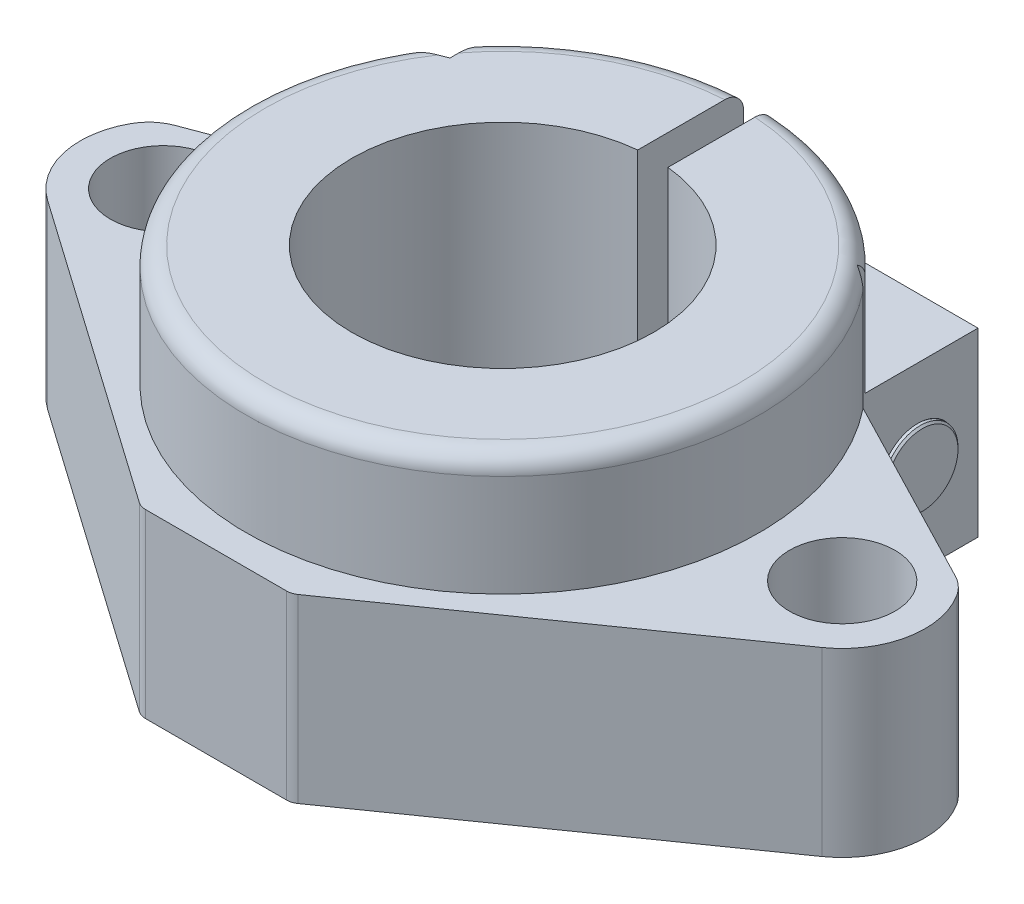
SolidWorks part; units mm, degrees
other "Markup1"
sketch "Sketch30" plane through (-28, 20, 19) normal (-0.8662, 0.4948, 0.0704) x (0.294, 0.3906, 0.8723)
ref_plane "Front Plane" through (0, 0, 0) normal (0, 0, 1) x (1, 0, 0)
ref_plane "Top Plane" through (0, 0, 0) normal (0, 1, 0) x (1, 0, 0)
ref_plane "Right Plane" through (0, 0, 0) normal (1, 0, 0) x (0, 0, -1)
sketch "Sketch1" plane through (0, 0, 0) normal (0, 1, 0) x (1, 0, 0)
  line L0 (0, 23.9567) -> (0, -22.6932) construction
  line L1 (-26.4411, 0) -> (25.427, 0) construction
  line L2 (5, -19) -> (-5, -19)
  line L3 (12.5, 19) -> (-12.5, 19)
  line L4 (-12.5, 19) -> (-26.5485, 3.7229)
  line L5 (-5, -19) -> (-25.6594, -4.502)
  line L6 (5, -19) -> (25.6594, -4.502)
  line L7 (12.5, 19) -> (26.5485, 3.7229)
  circle A1 centre (0, 0) radius 10 construction
  circle A2 centre (-22.5, 0) radius 3.5
  arc A3 (-26.5485, 3.7229) -> (-25.6594, -4.502) centre (-22.5, 0) ccw
  circle A4 centre (22.5, 0) radius 3.5
  arc A5 (26.5485, 3.7229) -> (25.6594, -4.502) centre (22.5, 0) cw
  point P20 (0, -19)
  point P21 (0, 19)
  dimension "D1" = 20
  dimension "D2" = 7
  dimension "D4" = 11
  dimension "D3" = 22.5
  dimension "D5" = 25
  dimension "D6" = 10
  dimension "D7" = 19
  dimension "D8" = 19
extrude "Boss-Extrude1" add sketch "Sketch1" along normal blind 12
sketch "Sketch3" plane through (0, 12, 0) normal (0, 1, 0) x (1, 0, 0)
  circle A0 centre (0, 0) radius 17
  dimension "D1" = 34
extrude "Boss-Extrude2" add sketch "Sketch3" along normal blind 8
fillet "Fillet1" radius 1.25 1 edges at (0, 20, 17)
sketch "Sketch2" plane through (0, 12, 0) normal (0, 1, 0) x (1, 0, 0)
  line L0 (12.5, 19) -> (12.5, 11)
  line L1 (12.5, 11) -> (26.5485, 3.7229)
  line L2 (26.5485, 3.7229) -> (12.5, 19)
  line L3 (-12.5, 19) -> (-12.5, 8.9996)
  line L4 (-12.5, 8.9996) -> (-26.5485, 3.7229)
  line L5 (-26.5485, 3.7229) -> (-12.5, 19)
  dimension "D1" = 8
  dimension "D2" = 10.0004
extrude "Cut-Extrude1" cut sketch "Sketch2" against normal through all both and the other way through all
sketch "Sketch4" plane through (0, 20, 0) normal (0, 1, 0) x (1, 0, 0)
  circle A0 centre (0, 0) radius 10
  dimension "D1" = 20
extrude "Cut-Extrude2" cut sketch "Sketch4" against normal through all both and the other way through all
sketch "Sketch5" plane through (0, 20, 0) normal (0, 1, 0) x (1, 0, 0)
  line L0 (0, 21.2575) -> (0, -21.4313) construction
  line L2 (1, 0) -> (-1, 0)
  line L3 (1, 0) -> (1, 20)
  line L4 (1, 20) -> (-1, 20)
  line L5 (-1, 0) -> (-1, 20)
  line L6 (1, 0) -> (-1, 20) construction
  line L7 (1, 20) -> (-1, 0) construction
  circle A0 centre (0, 0) radius 10 construction
  point P3 (0, 10)
  dimension "D1" = 2
  dimension "D2" = 20
extrude "Cut-Extrude3" cut sketch "Sketch5" against normal through all both
sketch "Sketch7" plane through (-12.5, 0, 0) normal (-1, 0, 0) x (0, 0, 1)
  line L0 (-8.9996, 0) -> (-19, 0) construction
  line L1 (-19, 12) -> (-19, 0) construction
  circle A0 centre (-15, 6) radius 3
  dimension "D1" = 6
  dimension "D2" = 6
  dimension "D3" = 4
extrude "Cut-Extrude4" cut sketch "Sketch7" against normal blind 12.5
fillet "Fillet2" radius 3 2 edges at (-26.5485, 6, -3.7229) (26.5485, 6, -3.7229)
fillet "Fillet3" radius 1 2 edges at (-5, 6, 19) (5, 6, 19)
hole_wizard "M5 Tapped Hole2" positions "Sketch15" profile "Sketch16" tap size "M5" standard "ISO" end condition through all
sketch "Sketch15" plane through (12.5, 0, 0) normal (1, 0, 0) x (0, 0, -1)
  line L0 (19, 12) -> (19, 0) construction
  line L1 (19, 0) -> (11, 0) construction
  point P0 (15, 6)
  dimension "D1" = 4
  dimension "D2" = 6
sketch "Sketch16" plane through (12.5, 6, -15) normal (0, 1, 0) x (0, 0, -1)
  line L0 (0, 0) -> (0, 40.5)
  line L1 (0, 40.5) -> (2.1, 40.5)
  line L2 (2.1, 40.5) -> (2.1, 0.425)
  line L3 (2.1, 0.425) -> (2.525, 0)
  line L5 (2.525, 0) -> (0, 0)
  line L6 (-2.1, 0.425) -> (-2.525, 0) construction
  line L11 (0, -6.35) -> (0, 107.95) construction
  dimension "Thru Tap Drill Dia." = 4.2
  dimension "Thru Tap Drill Depth" = 40.5
  dimension "Near C'Sink Dia." = 5.05
  dimension "Near C'Sink Angle" = 90
cosmetic thread "Hole Thread2" parameters "D2"=5
ref_plane "Plane3" through (-12.7, 0, 0) normal (-1, 0, 0) x (0, 0, 1)
sketch "Sketch26" plane through (-12.7, 0, 0) normal (-1, 0, 0) x (0, 0, 1)
  circle A0 centre (-15, 6) radius 2.5
  dimension "D1" = 5
extrude "Boss-Extrude4" add sketch "Sketch26" along normal blind 0.001 and the other way blind 25.5 separate body
sketch "Sketch28" plane through (-12.701, 0, 0) normal (-1, 0, 0) x (0, 0, 1)
  circle A0 centre (-15, 6) radius 4
  dimension "D1" = 8
extrude "Boss-Extrude5" add sketch "Sketch28" along normal blind 5
chamfer "Chamfer1" distance 0.125 angle 45 1 edges at (12.8, 6, -12.5)
sketch "Sketch29" plane through (-17.701, 0, 0) normal (-1, 0, 0) x (0, 0, 1)
  line L1 (-15, 8.3094) -> (-17, 7.1547)
  line L2 (-17, 7.1547) -> (-17, 4.8453)
  line L3 (-17, 4.8453) -> (-15, 3.6906)
  line L4 (-15, 3.6906) -> (-13, 4.8453)
  line L5 (-13, 4.8453) -> (-13, 7.1547)
  line L6 (-13, 7.1547) -> (-15, 8.3094)
  circle A0 centre (-15, 6) radius 2 construction
extrude "Cut-Extrude5" cut sketch "Sketch29" against normal blind 3
fillet "Fillet4" radius 0.75 1 edges at (-17.701, 6, -11)
